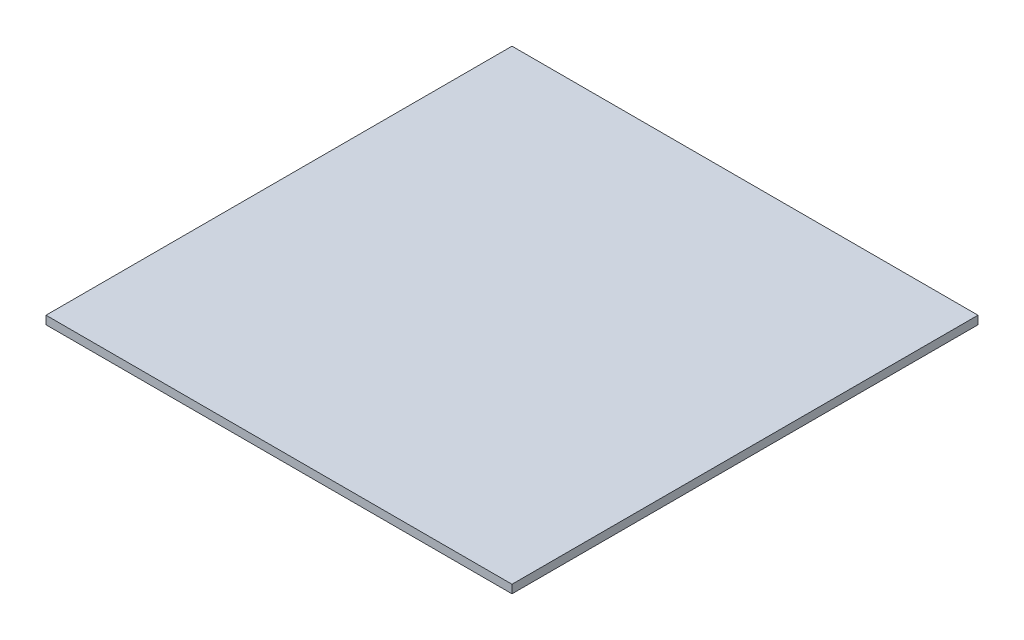
SolidWorks part; units mm, degrees
ref_plane "Płaszczyzna przednia" through (0, 0, 0) normal (0, 0, 1) x (1, 0, 0)
ref_plane "Płaszczyzna górna" through (0, 0, 0) normal (0, 1, 0) x (1, 0, 0)
ref_plane "Płaszczyzna prawa" through (0, 0, 0) normal (1, 0, 0) x (0, 0, -1)
sketch "Szkic1" plane through (0, 0, 0) normal (0, 1, 0) x (1, 0, 0)
  line L1 (-280, -280) -> (280, -280)
  line L2 (-280, -280) -> (-280, 280)
  line L3 (-280, 280) -> (280, 280)
  line L4 (280, -280) -> (280, 280)
  line L5 (-280, -280) -> (280, 280) construction
  line L6 (-280, 280) -> (280, -280) construction
  point P0 (0, 0)
  dimension "D1" = 560
  dimension "D2" = 560
extrude "Dodanie-wyciągnięcie2" add sketch "Szkic1" along normal blind 10
